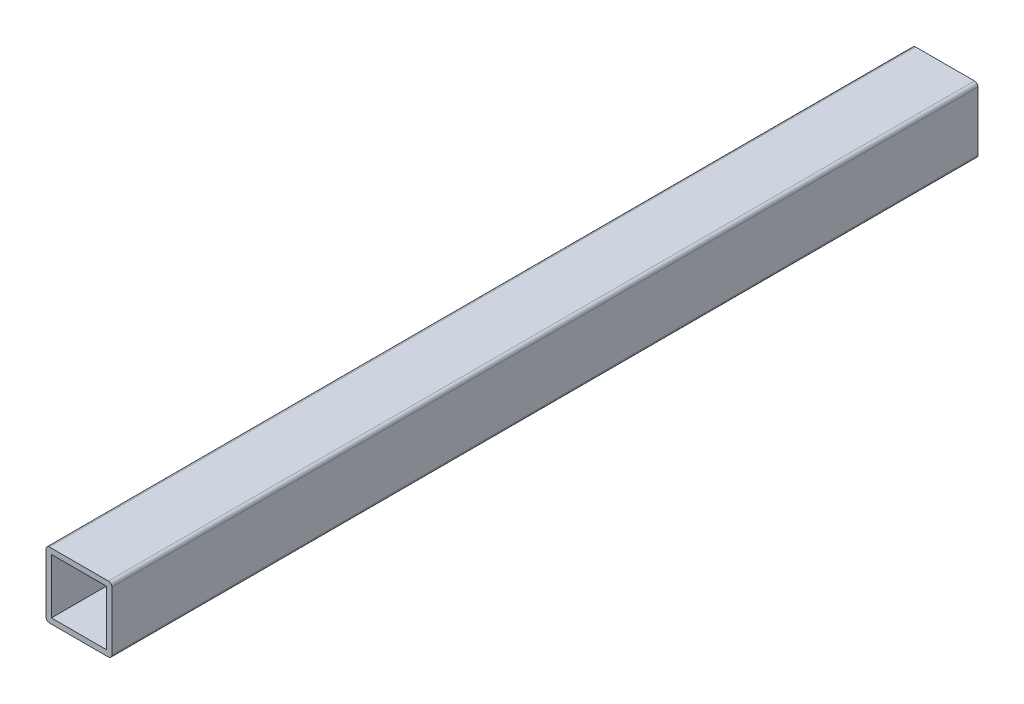
SolidWorks part; units mm, degrees
ref_plane "정면" through (0, 0, 0) normal (0, 0, 1) x (1, 0, 0)
ref_plane "윗면" through (0, 0, 0) normal (0, 1, 0) x (1, 0, 0)
ref_plane "우측면" through (0, 0, 0) normal (1, 0, 0) x (0, 0, -1)
sketch "스케치1" plane through (0, 0, 0) normal (0, 0, 1) x (1, 0, 0)
  line L1 (0, 0) -> (19, 0)
  line L2 (0, 0) -> (0, -19)
  line L3 (0, -19) -> (19, -19)
  line L4 (19, 0) -> (19, -19)
  line L5 (1.56, -1.56) -> (17.44, -1.56)
  line L6 (1.56, -1.56) -> (1.56, -17.44)
  line L7 (1.56, -17.44) -> (17.44, -17.44)
  line L8 (17.44, -1.56) -> (17.44, -17.44)
  dimension "D1" = 19
  dimension "D2" = 19
  dimension "D3" = 15.88
  dimension "D4" = 15.88
  dimension "D5" = 1.56
  dimension "D6" = 1.56
extrude "보스-돌출1" add sketch "스케치1" along normal blind 900
fillet "필렛2" radius 1 4 edges at (0, -19, 450) (0, 0, 450) (19, -19, 450) (19, 0, 450)
sketch "스케치2" plane through (19, 0, 0) normal (1, 0, 0) x (0, 0, -1)
  line L5 (-900, 0) -> (0, 0) construction
  line L6 (-900, -19) -> (-250, -19)
  line L7 (-900, -19) -> (-900, 0)
  line L8 (-900, 0) -> (-250, 0)
  line L9 (-250, -19) -> (-250, 0)
  dimension "D1" = 250
extrude "컷-돌출2" cut sketch "스케치2" against normal blind 51 contours L9 L8 L7 L6
